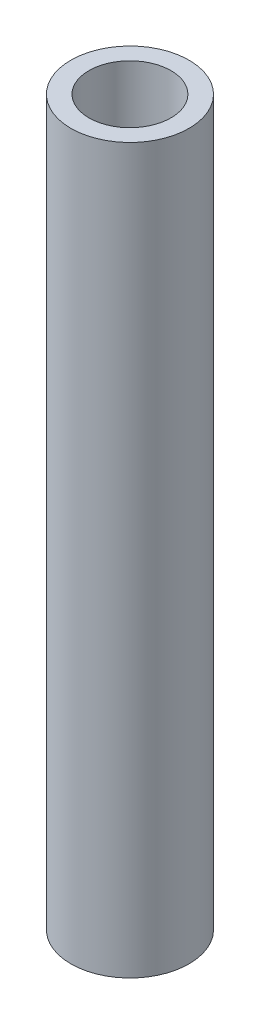
SolidWorks part; units mm, degrees
ref_plane "Front Plane" through (0, 0, 0) normal (0, 0, 1) x (1, 0, 0)
ref_plane "Top Plane" through (0, 0, 0) normal (0, 1, 0) x (1, 0, 0)
ref_plane "Right Plane" through (0, 0, 0) normal (1, 0, 0) x (0, 0, -1)
sketch "Sketch1" plane through (0, 0, 0) normal (0, 1, 0) x (1, 0, 0)
  circle A0 centre (0, 0) radius 2.159
  circle A1 centre (0, 0) radius 3.1115
  dimension "D1" = 4.318
  dimension "D2" = 6.223
extrude "Boss-Extrude1" add sketch "Sketch1" along normal mid plane 38.1
